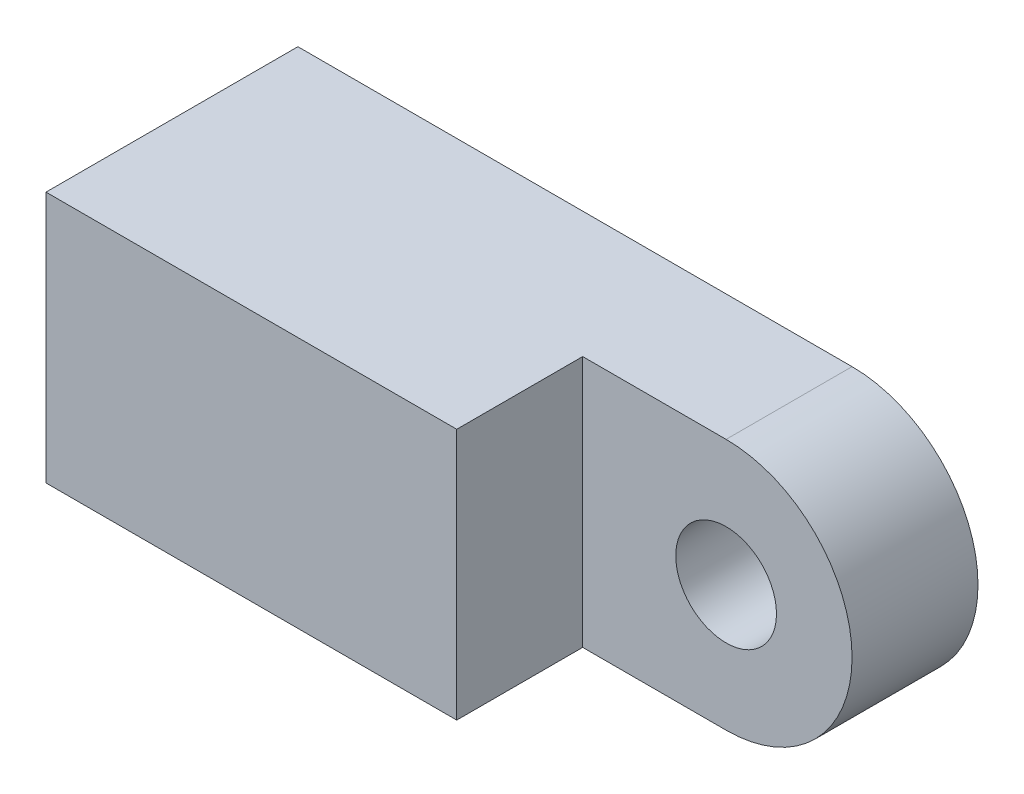
SolidWorks part; units mm, degrees
ref_plane "Front Plane" through (0, 0, 0) normal (0, 0, 1) x (1, 0, 0)
ref_plane "Top Plane" through (0, 0, 0) normal (0, 1, 0) x (1, 0, 0)
ref_plane "Right Plane" through (0, 0, 0) normal (1, 0, 0) x (0, 0, -1)
sketch "Sketch1" plane through (0, 0, 0) normal (0, 0, 1) x (1, 0, 0)
  line L0 (0, -10.8917) -> (2, -10.8917)
  line L1 (-20, -0.8917) -> (2, -0.8917)
  line L2 (-20, -0.8917) -> (-20, -10.8917)
  line L3 (-20, -10.8917) -> (0, -10.8917)
  arc A0 (2, -10.8917) -> (2, -0.8917) centre (2, -5.8917) ccw
  dimension "D3" = 5
  dimension "D1" = 20
  dimension "D2" = 10
  dimension "D4" = 2
extrude "Boss-Extrude1" add sketch "Sketch1" along normal blind 10
sketch "Sketch2" plane through (0, 0, 10) normal (0, 0, 1) x (1, 0, 0)
  circle A0 centre (2, -5.8917) radius 2
  arc A2 (2, -10.8917) -> (2, -0.8917) centre (2, -5.8917) ccw construction
  dimension "D1" = 4
extrude "Cut-Extrude1" cut sketch "Sketch2" against normal blind 30
sketch "Sketch4" plane through (0, 0, 10) normal (0, 0, 1) x (1, 0, 0)
  line L0 (2, -0.8917) -> (-20, -0.8917) construction
  line L1 (-3.6937, -0.8917) -> (15.0638, -0.8917)
  line L2 (-3.6937, -0.8917) -> (-3.6937, -10.9746)
  line L3 (-3.6937, -10.9746) -> (15.0638, -10.9746)
  line L4 (15.0638, -0.8917) -> (15.0638, -10.9746)
extrude "Cut-Extrude3" cut sketch "Sketch4" against normal blind 5
